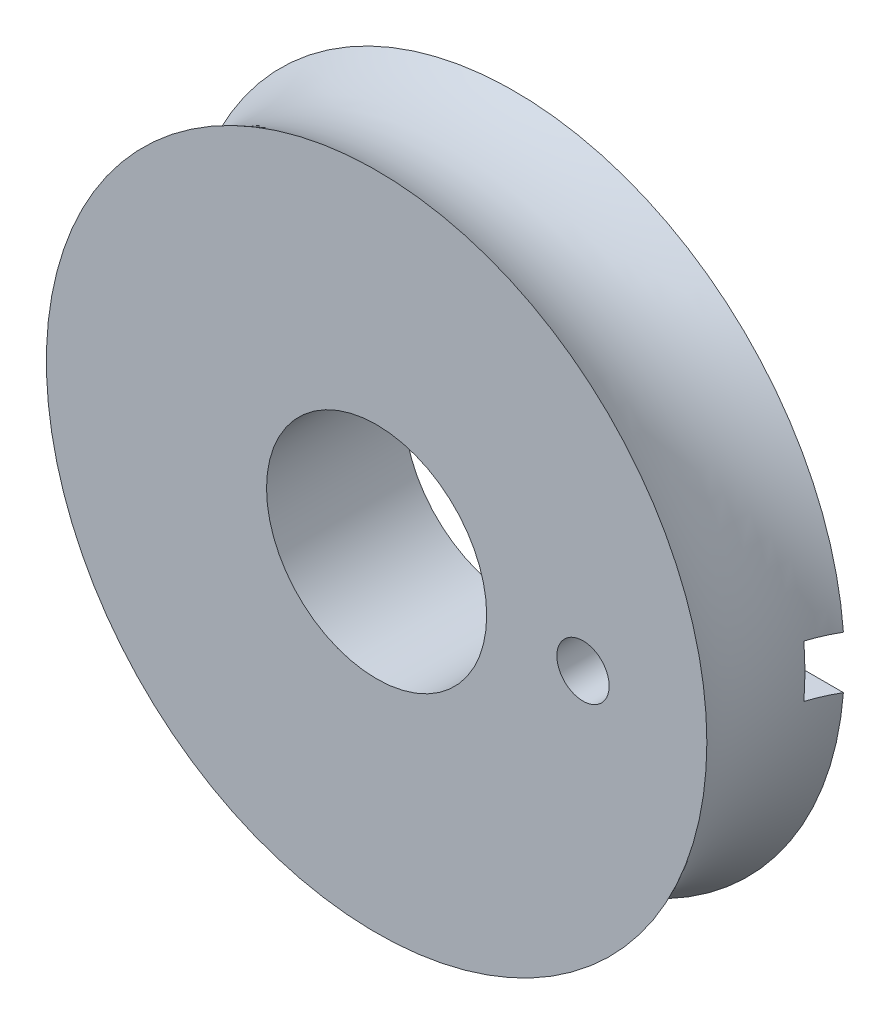
SolidWorks part; units mm, degrees
ref_plane "Plan de face" through (0, 0, 0) normal (0, 0, 1) x (1, 0, 0)
ref_plane "Plan de dessus" through (0, 0, 0) normal (0, 1, 0) x (1, 0, 0)
ref_plane "Plan de droite" through (0, 0, 0) normal (1, 0, 0) x (0, 0, -1)
sketch "Esquisse1" plane through (0, 0, 0) normal (0, 1, 0) x (1, 0, 0)
  line L0 (0, 0) -> (0, 5)
  line L1 (0, 5) -> (12, 5)
  line L2 (0, 0) -> (12, 0)
  arc A1 (12, 5) -> (12, 0) centre (16.3301, 2.5) ccw
  dimension "D1" = 5
  dimension "D2" = 12
  dimension "D3" = 5
revolve "Révolution1" add sketch "Esquisse1" angle 360 about L0
sketch "Esquisse2" plane through (0, 0, -5) normal (0, 0, -1) x (-1, 0, 0)
  circle A0 centre (0, 0) radius 4
  dimension "D1" = 8
extrude "Enlèv. mat.-Extru.1" cut sketch "Esquisse2" against normal blind 10
sketch "Esquisse3" plane through (0, 0, -5) normal (0, 0, -1) x (-1, 0, 0)
  circle A0 centre (-7.5, 0) radius 0.95
  point P2 (0, 0)
  dimension "D1" = 1.9
  dimension "D2" = 7.5
extrude "Enlèv. mat.-Extru.2" cut sketch "Esquisse3" against normal blind 5
sketch "Esquisse5" plane through (0, 0, -5) normal (0, 0, -1) x (-1, 0, 0)
  line L1 (-12.5, 0.95) -> (-7.5, 0.95)
  line L2 (-12.5, 0.95) -> (-12.5, -0.95)
  line L3 (-12.5, -0.95) -> (-7.5, -0.95)
  line L4 (-7.5, 0.95) -> (-7.5, -0.95)
  circle A0 centre (-7.5, 0) radius 0.95 construction
  dimension "D1" = 1.9
  dimension "D2" = 5
extrude "Enlèv. mat.-Extru.4" cut sketch "Esquisse5" against normal blind 1
